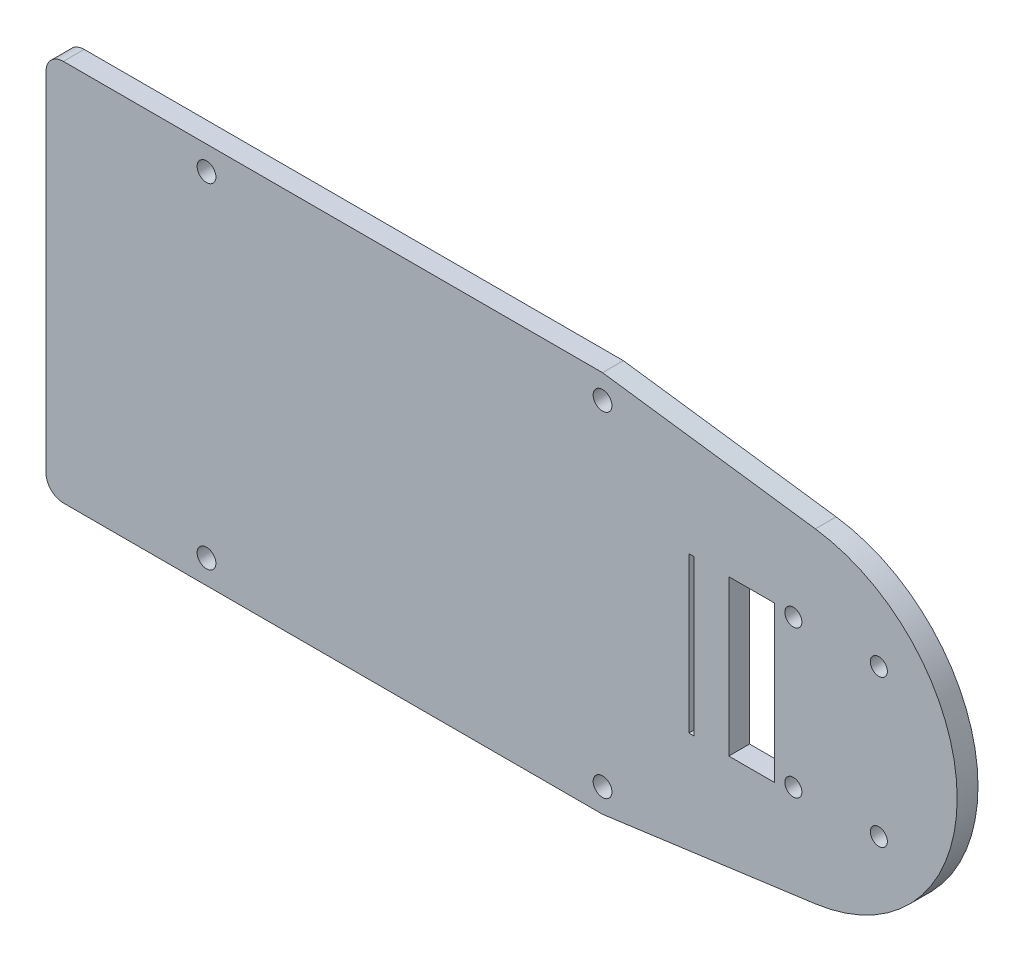
SolidWorks part; units mm, degrees
ref_plane "Front Plane" through (0, 0, 0) normal (0, 0, 1) x (1, 0, 0)
ref_plane "Top Plane" through (0, 0, 0) normal (0, 1, 0) x (1, 0, 0)
ref_plane "Right Plane" through (0, 0, 0) normal (1, 0, 0) x (0, 0, -1)
sketch "Sketch1" plane through (0, 0, 0) normal (0, 0, 1) x (1, 0, 0)
  line L0 (-2.1296, -12.975) -> (62.6404, -12.975) construction
  line L1 (-2.125, 12.025) -> (-2.1343, -37.975) construction
  line L2 (0.875, -40.975) -> (79.875, -40.9843) construction
  line L4 (0.4104, 15.0296) -> (60.1004, 15.0296)
  line L5 (-2.1296, 12.4896) -> (-2.1296, -38.4396)
  line L6 (0.4104, -40.9796) -> (60.1004, -40.9796)
  line L7 (62.6404, 12.4896) -> (62.6404, -38.4396)
  line L9 (40.375, 15.0296) -> (40.375, -40.9796) construction
  line L11 (79.875, 15.025) -> (0.875, 15.0343) construction
  circle A0 centre (1.375, 11.525) radius 1.375
  circle A1 centre (59.375, 11.525) radius 1.375
  circle A2 centre (59.375, -37.475) radius 1.375
  circle A3 centre (1.375, -37.475) radius 1.375
  arc A4 (60.1004, 15.0296) -> (62.6404, 12.4896) centre (60.1004, 12.4896) cw
  arc A5 (62.6404, -38.4396) -> (60.1004, -40.9796) centre (60.1004, -38.4396) cw
  arc A6 (0.4104, -40.9796) -> (-2.1296, -38.4396) centre (0.4104, -38.4396) cw
  arc A7 (-2.1296, 12.4896) -> (0.4104, 15.0296) centre (0.4104, 12.4896) cw
  dimension "D1" = 2.54
  dimension "D2" = 2.75
  dimension "D3" = 2.75
  dimension "D4" = 2.75
  dimension "D5" = 2.75
  dimension "D6" = 64.77
extrude "Boss-Extrude1" add sketch "Sketch1" against normal blind 3.048 contours L5 A6 L6 A5 L7 A4 L4 A7
sketch "Sketch2" plane through (0, 0, 0) normal (0, 0, 1) x (1, 0, 0)
  line L0 (19.8603, -24.3521) -> (26.5603, -24.3521)
  line L1 (19.8603, -24.3521) -> (19.8603, -1.5979)
  line L2 (19.8603, -1.5979) -> (26.5603, -1.5979)
  line L3 (26.5603, -24.3521) -> (26.5603, -1.5979)
  line L4 (-2.1296, 12.4896) -> (-2.1296, -38.4396) construction
  line L5 (62.6404, -38.4396) -> (62.6404, 12.4896) construction
  line L6 (29.3152, -23.5746) -> (29.3152, -2.0017) construction
  line L7 (14.0183, -24.3521) -> (14.7803, -24.3521)
  line L8 (26.5603, -12.975) -> (19.8603, -12.975) construction
  line L9 (62.6404, -12.975) -> (-2.1296, -12.975) construction
  line L13 (14.0183, -24.3521) -> (14.0183, -1.5979)
  line L14 (14.0183, -1.5979) -> (14.7803, -1.5979)
  line L15 (14.7803, -24.3521) -> (14.7803, -1.5979)
  line L16 (14.0183, -24.3521) -> (14.7803, -1.5979) construction
  line L17 (14.0183, -1.5979) -> (14.7803, -24.3521) construction
  circle A0 centre (29.3152, -2.0017) radius 1.25
  circle A1 centre (41.8388, -2.0017) radius 1.25
  circle A2 centre (41.8388, -23.5746) radius 1.25
  circle A3 centre (29.3152, -23.5746) radius 1.25
  circle A4 centre (29.3152, -12.9755) radius 23.999 construction
  point P12 (14.3993, -12.975)
  dimension "D1" = 2.5
  dimension "D2" = 2.5
  dimension "D3" = 2.5
  dimension "D4" = 2.5
  dimension "D5" = 6.7
  dimension "D6" = 22.7542
  dimension "D8" = 5.08
  dimension "D9" = 0.762
  dimension "D11" = 2.7549
  dimension "D12" = 0.7775
  dimension "D13" = 21.5729
  dimension "D14" = 12.5236
extrude "Cut-Extrude1" cut sketch "Sketch2" against normal through all
sketch "Sketch3" plane through (0, 0, 0) normal (0, 0, 1) x (1, 0, 0)
  line L0 (14.0183, -1.5979) -> (14.0183, -24.3521) construction
  line L1 (14.7803, -1.5979) -> (14.0183, -1.5979) construction
  line L5 (-37.625, 15.0296) -> (-37.625, -40.9796) construction
  line L6 (-80.1296, 12.4896) -> (-80.1296, -38.4396)
  line L7 (2.3396, -40.9796) -> (-77.5896, -40.9796)
  line L8 (4.8796, 12.4896) -> (4.8796, -38.4396)
  line L9 (2.3396, 15.0296) -> (-77.5896, 15.0296)
  line L10 (4.8796, -12.975) -> (-80.1296, -12.975) construction
  arc A8 (4.8796, 12.4896) -> (2.3396, 15.0296) centre (2.3396, 12.4896) ccw
  arc A9 (2.3396, -40.9796) -> (4.8796, -38.4396) centre (2.3396, -38.4396) ccw
  arc A10 (-80.1296, -38.4396) -> (-77.5896, -40.9796) centre (-77.5896, -38.4396) ccw
  arc A11 (-77.5896, 15.0296) -> (-80.1296, 12.4896) centre (-77.5896, 12.4896) ccw
  circle A12 centre (1.375, -37.475) radius 1.375
  circle A13 centre (-56.625, -37.475) radius 1.375
  circle A14 centre (-56.625, 11.525) radius 1.375
  circle A15 centre (1.375, 11.525) radius 1.375
  dimension "D1" = 2.75
  dimension "D2" = 2.54
  dimension "D3" = 85.0093
  dimension "D4" = 23.5046
  dimension "D5" = 28.0046
  dimension "D6" = 39
  dimension "D7" = 24.5
  dimension "D9" = 24.5
extrude "Boss-Extrude2" add sketch "Sketch3" against normal through all
sketch "Sketch5" plane through (0, 0, -3.048) normal (0, 0, -1) x (-1, 0, 0)
  line L0 (-1.375, 15.0296) -> (-1.375, -40.9796) construction
  line L1 (77.5896, -40.9796) -> (-60.1004, -40.9796) construction
  line L2 (-60.1004, 15.0296) -> (77.5896, 15.0296) construction
  line L3 (-1.375, 15.0296) -> (-32.5383, 10.8061)
  line L4 (-1.375, -40.9796) -> (-32.5375, -36.7572)
  line L5 (-1.375, 15.0296) -> (-97.656, 15.0296)
  line L6 (-97.656, 15.0296) -> (-97.656, -40.9796)
  line L7 (-97.656, -40.9796) -> (-1.375, -40.9796)
  arc A0 (-32.5375, -36.7572) -> (-32.5383, 10.8061) centre (-29.3152, -12.9755) cw
extrude "Cut-Extrude3" cut sketch "Sketch5" against normal through all
